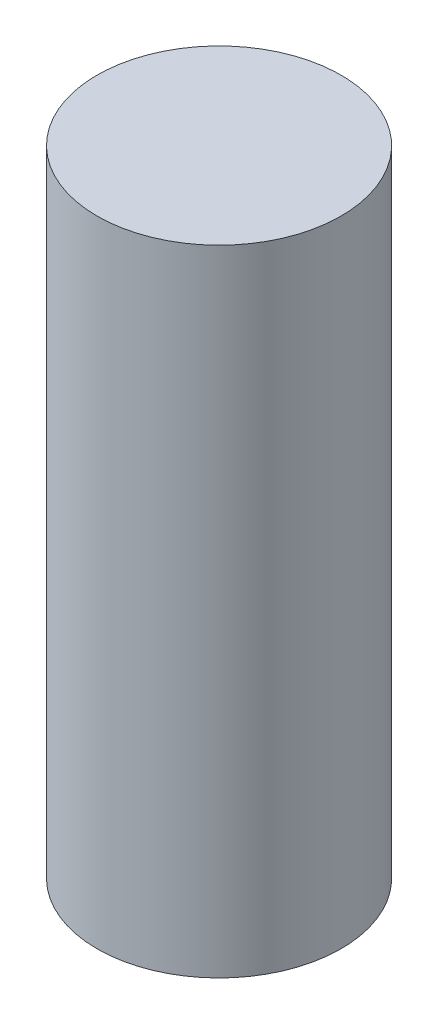
SolidWorks part; units mm, degrees
ref_plane "Front Plane" through (0, 0, 0) normal (0, 0, 1) x (1, 0, 0)
ref_plane "Top Plane" through (0, 0, 0) normal (0, 1, 0) x (1, 0, 0)
ref_plane "Right Plane" through (0, 0, 0) normal (1, 0, 0) x (0, 0, -1)
sketch "Sketch1" plane through (0, 0, 0) normal (0, 1, 0) x (1, 0, 0)
  circle A0 centre (0, 0) radius 0.5
  dimension "D1" = 1
extrude "Boss-Extrude1" add sketch "Sketch1" along normal blind 2.6
